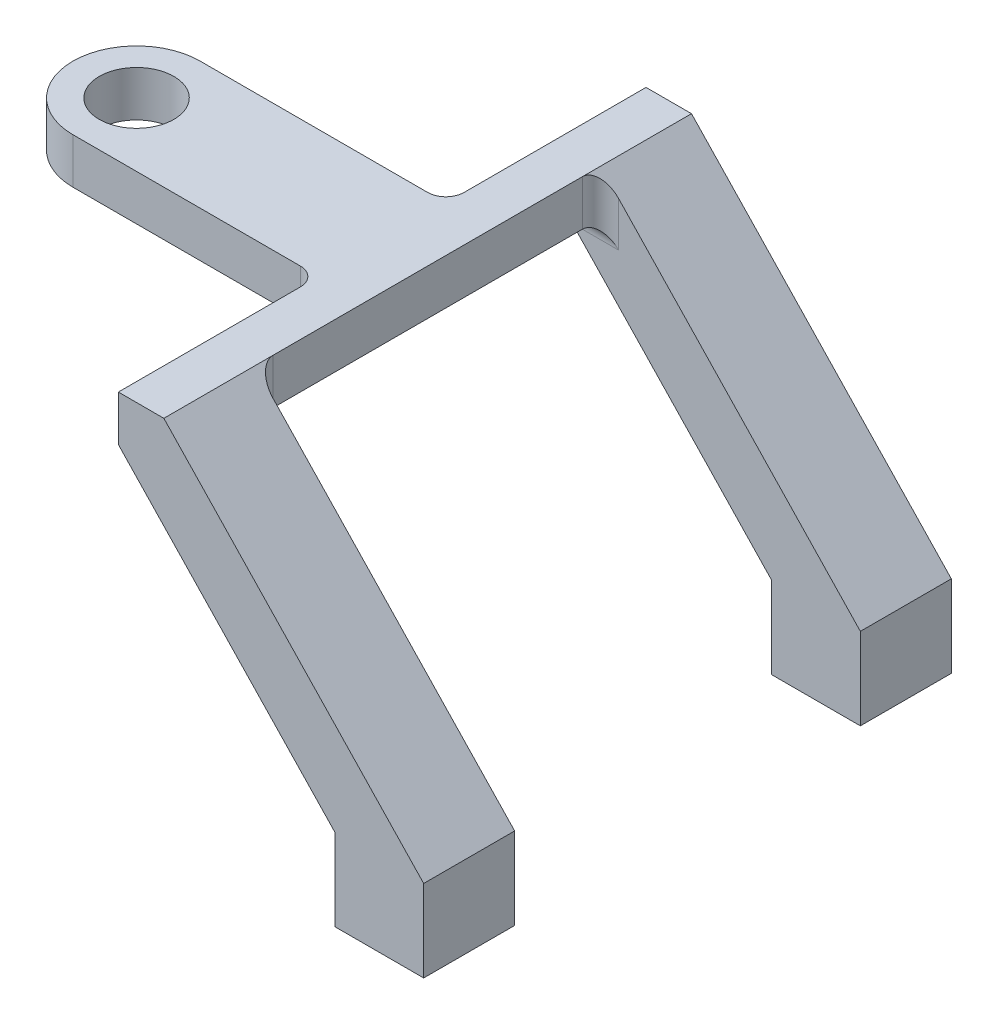
SolidWorks part; units mm, degrees
ref_plane "Front Plane" through (0, 0, 0) normal (0, 0, 1) x (1, 0, 0)
ref_plane "Top Plane" through (0, 0, 0) normal (0, 1, 0) x (1, 0, 0)
ref_plane "Right Plane" through (0, 0, 0) normal (1, 0, 0) x (0, 0, -1)
sketch "Sketch1" plane through (0, 0, 0) normal (0, 0, 1) x (1, 0, 0)
  line L0 (0, 0) -> (-12.3952, 0)
  line L1 (-12.3952, 0) -> (-12.3952, 11.43)
  line L2 (-12.3952, 11.43) -> (-42.6212, 43.18)
  line L3 (-42.6212, 43.18) -> (-42.6212, 49.53)
  line L4 (-42.6212, 49.53) -> (-36.2712, 49.53)
  line L5 (-36.2712, 49.53) -> (0, 11.43)
  line L6 (0, 11.43) -> (0, 0)
  dimension "D1" = 6.35
  dimension "D2" = 6.35
  dimension "D3" = 43.18
  dimension "D4" = 31.75
  dimension "D5" = 30.226
extrude "Boss-Extrude1" add sketch "Sketch1" along normal blind 12.7
sketch "Sketch2" plane through (0, 0, 12.7) normal (0, 0, 1) x (1, 0, 0)
  line L0 (-36.2712, 49.53) -> (-42.6212, 49.53) construction
  line L1 (-42.6212, 49.53) -> (-36.2712, 49.53)
  line L2 (-42.6212, 49.53) -> (-42.6212, 43.18)
  line L3 (-42.6212, 43.18) -> (-36.2712, 43.18)
  line L4 (-36.2712, 49.53) -> (-36.2712, 43.18)
extrude "Boss-Extrude2" add sketch "Sketch2" along normal blind 48.26
sketch "Sketch3" plane through (0, 0, 60.96) normal (0, 0, 1) x (1, 0, 0)
  line L0 (-42.6212, 43.18) -> (-12.3952, 11.43)
  line L1 (-12.3952, 11.43) -> (-12.3952, 0)
  line L2 (-12.3952, 0) -> (0, 0)
  line L3 (0, 0) -> (0, 11.43)
  line L4 (0, 11.43) -> (-36.2712, 49.53)
  line L5 (-36.2712, 49.53) -> (-42.6212, 49.53)
  line L6 (-42.6212, 49.53) -> (-42.6212, 43.18)
extrude "Boss-Extrude3" add sketch "Sketch3" along normal blind 12.7
sketch "Sketch4" plane through (0, 49.53, 0) normal (0, 1, 0) x (1, 0, 0)
  line L0 (-42.6212, -27.94) -> (-76.9112, -27.94)
  line L1 (-42.6212, -73.66) -> (-42.6212, 0) construction
  line L2 (-76.9112, -45.72) -> (-42.6212, -45.72)
  line L3 (-42.6212, -27.94) -> (-42.6212, -45.72)
  line L4 (-36.2712, -60.96) -> (-36.2712, -12.7) construction
  arc A0 (-76.9112, -27.94) -> (-76.9112, -45.72) centre (-76.9112, -36.83) ccw
  circle A1 centre (-76.9112, -36.83) radius 5.207
  point P9 (-36.2712, -36.83)
  point P10 (-42.6212, -36.83)
  dimension "D1" = 10.414
  dimension "D2" = 3.683
  dimension "D3" = 34.29
extrude "Boss-Extrude4" add sketch "Sketch4" against normal up to surface (6.35 mm away) up to face at (-39.4462, 43.18, 36.83)
fillet "Fillet1" radius 2.54 6 edges at (-36.2712, 46.355, 12.7) (-36.2712, 46.355, 60.96) (-42.6212, 46.355, 45.72) (-42.6212, 46.355, 27.94) (-39.4462, 43.18, 60.96) (-39.4462, 43.18, 12.7)
